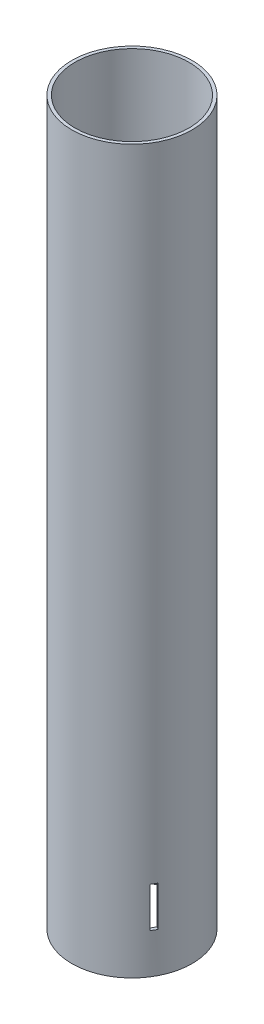
SolidWorks part; units mm, degrees
ref_plane "Front Plane" through (0, 0, 0) normal (0, 0, 1) x (1, 0, 0)
ref_plane "Top Plane" through (0, 0, 0) normal (0, 1, 0) x (1, 0, 0)
ref_plane "Right Plane" through (0, 0, 0) normal (1, 0, 0) x (0, 0, -1)
sketch "Sketch1" plane through (0, 0, 0) normal (0, 1, 0) x (1, 0, 0)
  circle A0 centre (0, 0) radius 36.1
  circle A1 centre (0, 0) radius 38.1
  dimension "D1" = 2
  dimension "D2" = 76.2
extrude "Boss-Extrude1" add sketch "Sketch1" along normal blind 457.2
sketch "Sketch2" plane through (0, 0, 0) normal (0, 0, 1) x (1, 0, 0)
  line L0 (0, 0) -> (0, 50.8) construction
  line L2 (-1.905, 50.8) -> (1.905, 50.8)
  line L3 (-1.905, 50.8) -> (-1.905, 25.4)
  line L4 (-1.905, 25.4) -> (1.905, 25.4)
  line L5 (1.905, 50.8) -> (1.905, 25.4)
  point P7 (0, 0)
  point P8 (0, 50.8)
  dimension "D1" = 3.81
  dimension "D2" = 25.4
  dimension "D3" = 25.4
extrude "Cut-Extrude1" cut sketch "Sketch2" against normal through all
pattern_circular "CirPattern1" count 3 every 120 about axis through (0, 0, 0) along (0, 1, 0) of "Cut-Extrude1"
